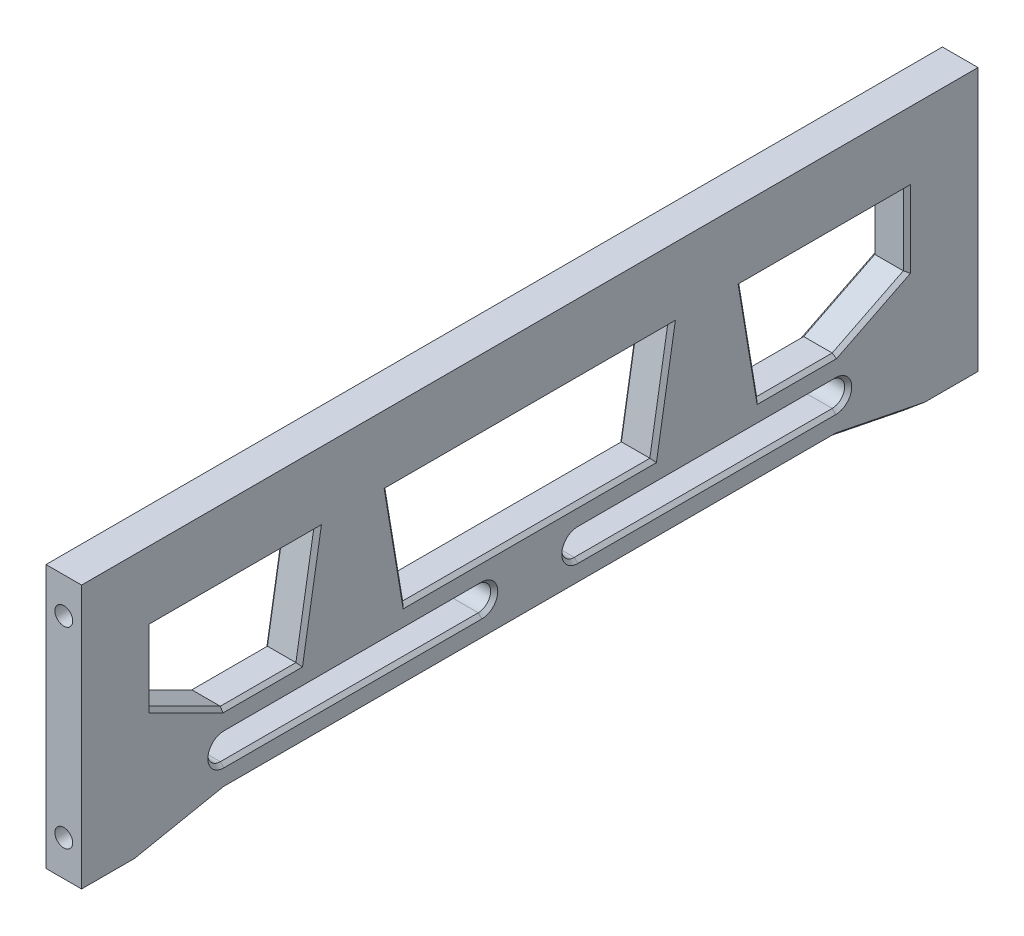
SolidWorks part; units mm, degrees
ref_plane "Alzado" through (0, 0, 0) normal (0, 0, 1) x (1, 0, 0)
ref_plane "Planta" through (0, 0, 0) normal (0, 1, 0) x (1, 0, 0)
ref_plane "Vista lateral" through (0, 0, 0) normal (1, 0, 0) x (0, 0, -1)
sketch "Croquis1" plane through (0, 0, 0) normal (0, 0, 1) x (1, 0, 0)
  line L1 (-2.5, -5) -> (2.5, -5)
  line L2 (-2.5, -5) -> (-2.5, 5)
  line L3 (-2.5, 5) -> (2.5, 5)
  line L4 (2.5, -5) -> (2.5, 5)
  line L5 (-2.5, -5) -> (2.5, 5) construction
  line L6 (-2.5, 5) -> (2.5, -5) construction
  point P0 (0, 0)
extrude "Saliente-Extruir1" add sketch "Croquis1" along normal blind 126
sketch "Croquis4" plane through (-2.5, 0, 0) normal (-1, 0, 0) x (0, 0, 1)
  line L3 (126, -5) -> (0, -5) construction
  line L7 (63, -5) -> (63, 5) construction
  line L8 (126, 5) -> (0, 5) construction
  line L17 (0, -5) -> (0, -32)
  line L18 (0, -32) -> (10, -32) construction
  line L19 (20, -30) -> (20, -20) construction
  line L20 (0, -5) -> (10, -5)
  line L21 (20, -30) -> (10, -32) construction
  line L22 (20, -30) -> (106, -30) construction
  line L23 (10, -5) -> (10, -15)
  line L24 (106, -20) -> (20, -20) construction
  line L25 (10, -15) -> (20, -20)
  line L27 (10, -15) -> (10, -5) construction
  line L28 (10, -15) -> (20, -20) construction
  line L29 (0, -32) -> (10, -32)
  line L30 (10, -32) -> (20, -30)
  line L31 (20, -30) -> (106, -30)
  line L32 (116, -15) -> (106, -20) construction
  line L33 (116, -15) -> (116, -5) construction
  line L34 (106, -30) -> (116, -32) construction
  line L35 (106, -30) -> (106, -20) construction
  line L36 (126, -32) -> (116, -32) construction
  line L37 (116, -32) -> (106, -30)
  line L38 (126, -32) -> (116, -32)
  line L39 (116, -15) -> (106, -20)
  line L40 (116, -5) -> (116, -15)
  line L41 (126, -5) -> (116, -5)
  line L42 (126, -5) -> (126, -32)
  line L43 (63, -20) -> (63, -30) construction
  line L46 (63, -25) -> (56.25, -25) construction
  line L47 (63, -25) -> (69.75, -25) construction
  line L48 (20, -25) -> (56.25, -25) construction
  line L49 (20, -23.25) -> (56.25, -23.25)
  line L50 (20, -26.75) -> (56.25, -26.75)
  line L51 (69.75, -25) -> (106, -25) construction
  line L52 (69.75, -23.25) -> (106, -23.25)
  line L53 (69.75, -26.75) -> (106, -26.75)
  line L54 (38.125, -25) -> (38.125, -5) construction
  line L55 (33.125, -5) -> (43.125, -5)
  line L57 (20, -20) -> (30.625, -20)
  line L58 (33.125, -5) -> (30.625, -20)
  line L59 (43.125, -5) -> (45.625, -20)
  line L60 (45.625, -20) -> (80.375, -20)
  line L61 (87.875, -25) -> (87.875, -5) construction
  line L62 (82.875, -5) -> (80.375, -20)
  line L63 (92.875, -5) -> (95.375, -20)
  line L64 (106, -20) -> (95.375, -20)
  line L65 (92.875, -5) -> (82.875, -5)
  arc A2 (20, -23.25) -> (20, -26.75) centre (20, -25) ccw
  arc A3 (56.25, -26.75) -> (56.25, -23.25) centre (56.25, -25) ccw
  arc A4 (69.75, -23.25) -> (69.75, -26.75) centre (69.75, -25) ccw
  arc A5 (106, -26.75) -> (106, -23.25) centre (106, -25) ccw
  point P2 (87.875, -25)
  point P14 (63, -20)
  point P26 (63, -30)
  point P33 (38.125, -25)
  point P46 (38.125, -5)
  point P49 (38.125, -20)
  point P55 (87.875, -20)
extrude "Saliente-Extruir2" add sketch "Croquis4" against normal blind 5
sketch "Croquis2" plane through (0, 0, 126) normal (0, 0, 1) x (1, 0, 0)
  line L1 (0, -32) -> (0, -27) construction
  line L2 (2.5, -32) -> (-2.5, -32) construction
  circle A2 centre (0, 0) radius 1.25
  circle A4 centre (0, -27) radius 1.25
  point P0 (0, 0)
  point P5 (0, 0)
extrude "Cortar-Extruir1" cut sketch "Croquis2" against normal blind 10
sketch "Croquis3" plane through (0, 0, 0) normal (0, 0, -1) x (-1, 0, 0)
  line L1 (0, -32) -> (0, -27) construction
  line L2 (-2.5, -32) -> (2.5, -32) construction
  circle A0 centre (0, 0) radius 1.25
  circle A2 centre (0, -27) radius 1.25
  point P2 (0, 0)
  point P4 (0, 0)
  point P6 (0, 0)
extrude "Cortar-Extruir2" cut sketch "Croquis3" against normal blind 10
chamfer "Chaflán1" distance 0.5 angle 45 50 edges at (2.5, -5, 104.4375) (-2.5, -12.5, 94.125) (2.5, -12.5, 94.125) (-2.5, -20, 100.6875) (2.5, -20, 100.6875) (-2.5, -17.5, 111) (2.5, -17.5, 111) (-2.5, -10, 116) (2.5, -10, 116) (-2.5, -20, 25.3125) (2.5, -20, 25.3125) (-2.5, -17.5, 15) (2.5, -17.5, 15) (-2.5, -10, 10) (2.5, -10, 10) (-2.5, -12.5, 31.875) (2.5, -12.5, 31.875) (2.5, -5, 21.5625) (-2.5, -12.5, 44.375) (2.5, -12.5, 44.375) (2.5, -5, 63) (-2.5, -12.5, 81.625) (2.5, -12.5, 81.625) (-2.5, -20, 63) (2.5, -20, 63) (-2.5, -23.25, 38.125) (2.5, -23.25, 38.125) (-2.5, -25, 18.25) (2.5, -25, 18.25) (-2.5, -25, 58) (2.5, -25, 58) (-2.5, -26.75, 38.125) (2.5, -26.75, 38.125) (-2.5, -23.25, 87.875) (2.5, -23.25, 87.875) (-2.5, -25, 68) (2.5, -25, 68) (-2.5, -25, 107.75) (2.5, -25, 107.75) (-2.5, -26.75, 87.875) (2.5, -26.75, 87.875) (-2.5, -31, 15) (2.5, -31, 15) (-2.5, -30, 63) (2.5, -30, 63) (-2.5, -31, 111) (2.5, -31, 111) (-2.5, -5, 21.5625) (-2.5, -5, 104.4375) (-2.5, -5, 63)
